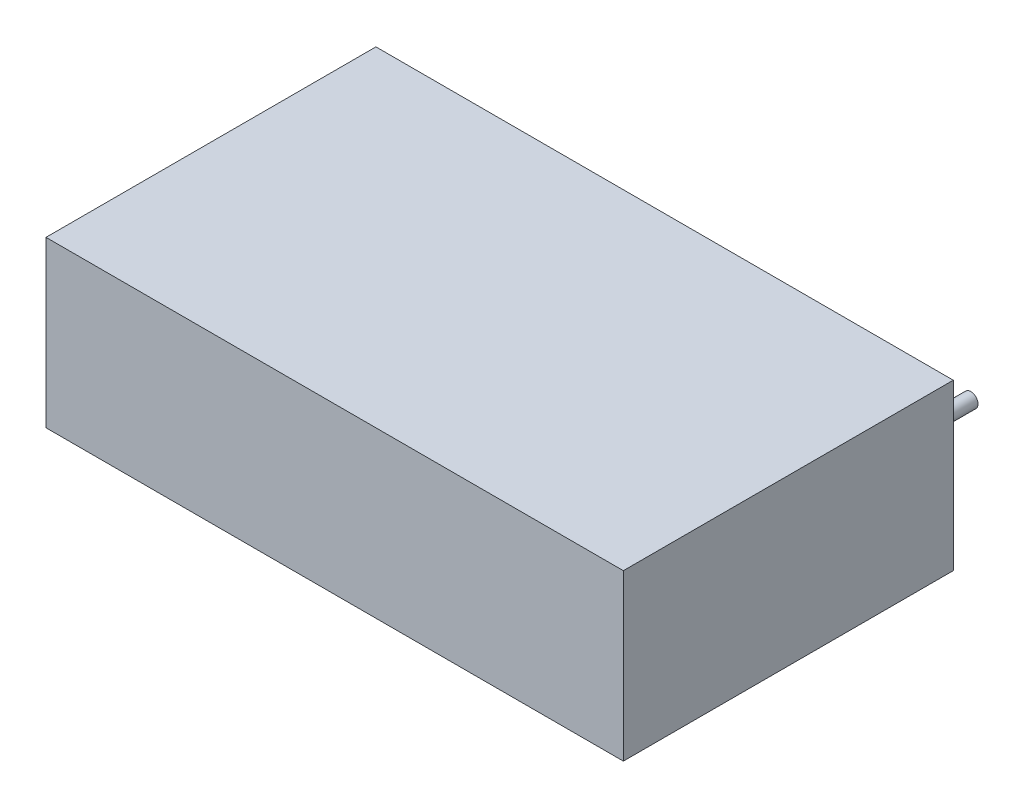
SolidWorks part; units mm, degrees
ref_plane "Plan de face" through (0, 0, 0) normal (0, 0, 1) x (1, 0, 0)
ref_plane "Plan de dessus" through (0, 0, 0) normal (0, 1, 0) x (1, 0, 0)
ref_plane "Plan de droite" through (0, 0, 0) normal (1, 0, 0) x (0, 0, -1)
sketch "Esquisse1" plane through (0, 0, 0) normal (0, 0, 1) x (1, 0, 0)
  line L1 (-14, -4) -> (14, -4)
  line L2 (-14, -4) -> (-14, 4)
  line L3 (-14, 4) -> (14, 4)
  line L4 (14, -4) -> (14, 4)
  line L5 (-14, -4) -> (14, 4) construction
  line L6 (-14, 4) -> (14, -4) construction
  point P0 (0, 0)
  dimension "D1" = 8
  dimension "D2" = 28
extrude "Boss.-Extru.1" add sketch "Esquisse1" along normal blind 16
sketch "Esquisse2" plane through (0, 0, 0) normal (0, 0, -1) x (-1, 0, 0)
  line L0 (-11.25, 0) -> (0, 0) construction
  line L1 (0, 0) -> (11.25, 0) construction
  circle A0 centre (-11.25, 0) radius 0.35
  circle A1 centre (11.25, 0) radius 0.35
  dimension "D1" = 0.7
  dimension "D2" = 22.5
extrude "Boss.-Extru.2" add sketch "Esquisse2" along normal blind 3.6
